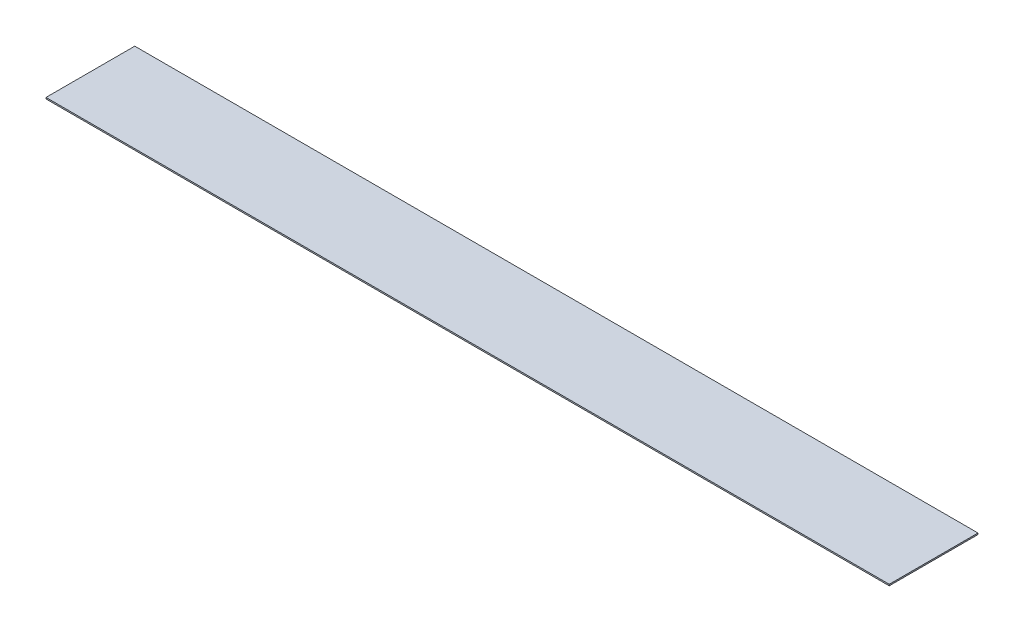
SolidWorks part; units mm, degrees
material "Nylon 101"
ref_plane "Front Plane" through (0, 0, 0) normal (0, 0, 1) x (1, 0, 0)
ref_plane "Top Plane" through (0, 0, 0) normal (0, 1, 0) x (1, 0, 0)
ref_plane "Right Plane" through (0, 0, 0) normal (1, 0, 0) x (0, 0, -1)
sketch "Sketch1" plane through (0, 0, 0) normal (0, 1, 0) x (1, 0, 0)
  line L1 (0, 0) -> (965.2, 0)
  line L2 (0, 0) -> (0, 101.6)
  line L3 (0, 101.6) -> (965.2, 101.6)
  line L4 (965.2, 0) -> (965.2, 101.6)
  dimension "D1" = 101.6
  dimension "D2" = 965.2
extrude "Boss-Extrude1" add sketch "Sketch1" along normal blind 1.5875
